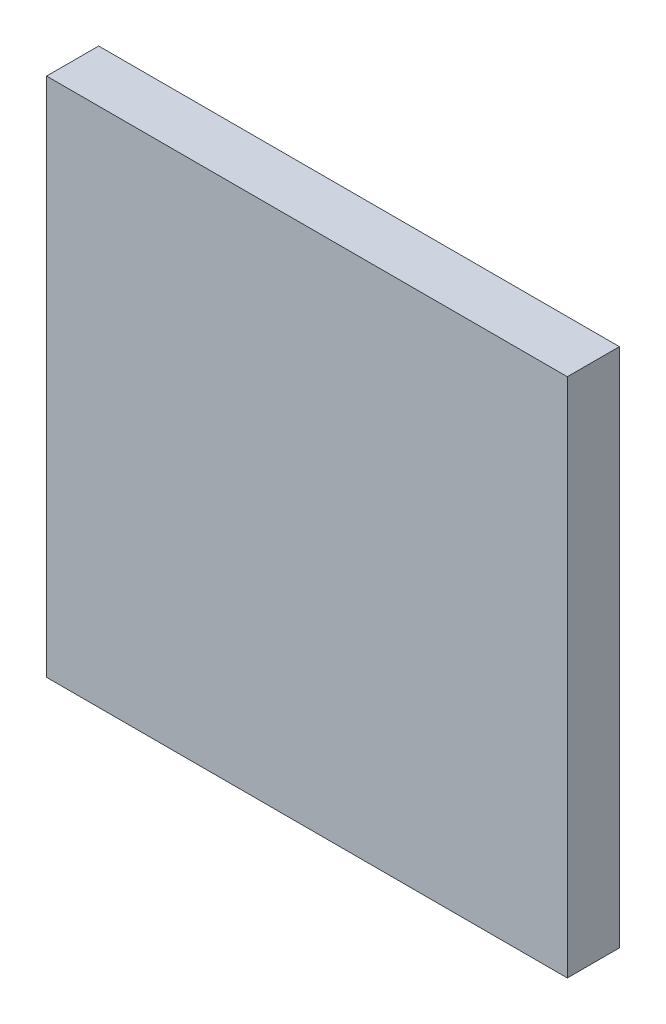
SolidWorks part; units mm, degrees
ref_plane "Plan de face" through (0, 0, 0) normal (0, 0, 1) x (1, 0, 0)
ref_plane "Plan de dessus" through (0, 0, 0) normal (0, 1, 0) x (1, 0, 0)
ref_plane "Plan de droite" through (0, 0, 0) normal (1, 0, 0) x (0, 0, -1)
sketch "Esquisse1" plane through (0, 0, 0) normal (0, 0, 1) x (1, 0, 0)
  line L1 (0, 0) -> (100, 0)
  line L2 (0, 0) -> (0, 100)
  line L3 (0, 100) -> (100, 100)
  line L4 (100, 0) -> (100, 100)
  dimension "D1" = 100
  dimension "D2" = 100
extrude "Boss.-Extru.1" add sketch "Esquisse1" along normal blind 10
